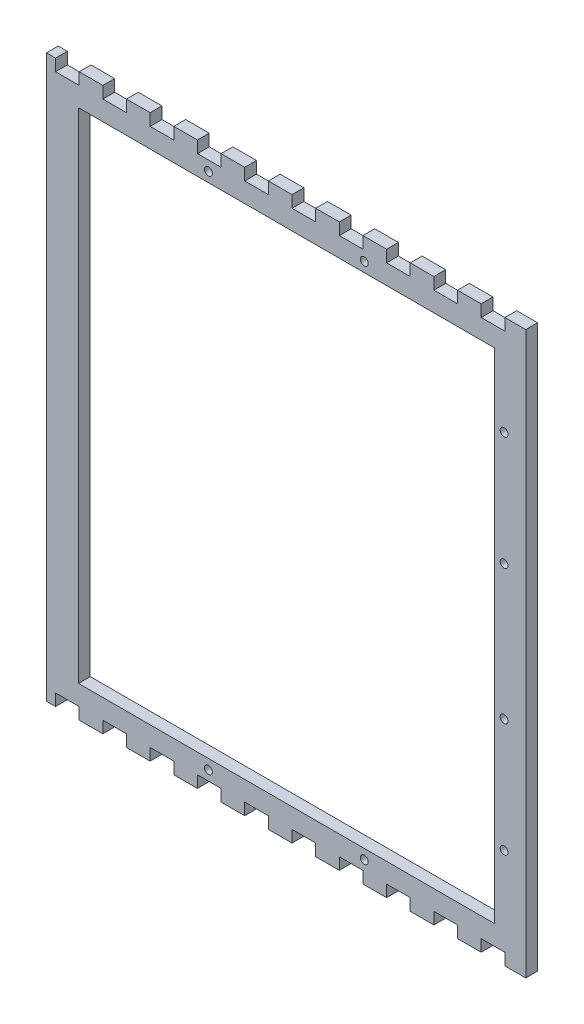
SolidWorks part; units mm, degrees
ref_plane "Front Plane" through (0, 0, 0) normal (0, 0, 1) x (1, 0, 0)
ref_plane "Top Plane" through (0, 0, 0) normal (0, 1, 0) x (1, 0, 0)
ref_plane "Right Plane" through (0, 0, 0) normal (1, 0, 0) x (0, 0, -1)
sketch "Model" plane through (0, 0, 0) normal (0, 0, 1) x (1, 0, 0)
  line L857 (1148.22, 22.8575) -> (1152.62, 22.8575)
  line L858 (1152.62, 22.8575) -> (1152.62, 28.5722)
  line L859 (1152.62, 28.5722) -> (1164.05, 28.5722)
  line L860 (1164.05, 28.5722) -> (1164.05, 22.8575)
  line L861 (1164.05, 22.8575) -> (1175.48, 22.8575)
  line L862 (1175.48, 22.8575) -> (1175.48, 28.5722)
  line L863 (1175.48, 28.5722) -> (1186.91, 28.5722)
  line L864 (1186.91, 28.5722) -> (1186.91, 22.8575)
  line L865 (1186.91, 22.8575) -> (1198.34, 22.8575)
  line L866 (1198.34, 22.8575) -> (1198.34, 28.5722)
  line L867 (1198.34, 28.5722) -> (1209.77, 28.5722)
  line L868 (1209.77, 28.5722) -> (1209.77, 22.8575)
  line L869 (1209.77, 22.8575) -> (1221.2, 22.8575)
  line L870 (1221.2, 22.8575) -> (1221.2, 28.5722)
  line L871 (1221.2, 28.5722) -> (1232.63, 28.5722)
  line L872 (1232.63, 28.5722) -> (1232.63, 22.8575)
  line L873 (1232.63, 22.8575) -> (1244.06, 22.8575)
  line L874 (1244.06, 22.8575) -> (1244.06, 28.5722)
  line L875 (1244.06, 28.5722) -> (1255.49, 28.5722)
  line L876 (1255.49, 28.5722) -> (1255.49, 22.8575)
  line L877 (1255.49, 22.8575) -> (1266.92, 22.8575)
  line L878 (1266.92, 22.8575) -> (1266.92, 28.5722)
  line L879 (1266.92, 28.5722) -> (1278.35, 28.5722)
  line L880 (1278.35, 28.5722) -> (1278.35, 22.8575)
  line L881 (1278.35, 22.8575) -> (1289.78, 22.8575)
  line L882 (1289.78, 22.8575) -> (1289.78, 28.5722)
  line L883 (1289.78, 28.5722) -> (1301.21, 28.5722)
  line L884 (1301.21, 28.5722) -> (1301.21, 22.8575)
  line L885 (1301.21, 22.8575) -> (1312.64, 22.8575)
  line L886 (1312.64, 22.8575) -> (1312.64, 28.5722)
  line L887 (1312.64, 28.5722) -> (1324.07, 28.5722)
  line L888 (1324.07, 28.5722) -> (1324.07, 22.8575)
  line L889 (1324.07, 22.8575) -> (1335.5, 22.8575)
  line L890 (1335.5, 22.8575) -> (1335.5, 28.5722)
  line L891 (1335.5, 28.5722) -> (1346.93, 28.5722)
  line L892 (1346.93, 28.5722) -> (1346.93, 22.8575)
  line L893 (1346.93, 22.8575) -> (1358.36, 22.8575)
  line L894 (1358.36, 22.8575) -> (1358.36, 28.5722)
  line L895 (1358.36, 28.5722) -> (1369.79, 28.5722)
  line L896 (1369.79, 28.5722) -> (1369.79, 22.8575)
  line L897 (1369.79, 22.8575) -> (1374.18, 22.8575)
  line L898 (1374.18, 22.8575) -> (1379.9, 22.8575)
  line L899 (1379.9, 22.8575) -> (1379.9, 28.5722)
  line L900 (1379.9, 28.5722) -> (1379.9, 288.572)
  line L901 (1379.9, 288.572) -> (1379.9, 294.287)
  line L902 (1379.9, 294.287) -> (1374.18, 294.287)
  line L903 (1374.18, 294.287) -> (1369.79, 294.287)
  line L904 (1369.79, 294.287) -> (1369.79, 288.572)
  line L905 (1369.79, 288.572) -> (1358.36, 288.572)
  line L906 (1358.36, 288.572) -> (1358.36, 294.287)
  line L907 (1358.36, 294.287) -> (1346.93, 294.287)
  line L908 (1346.93, 294.287) -> (1346.93, 288.572)
  line L909 (1346.93, 288.572) -> (1335.5, 288.572)
  line L910 (1335.5, 288.572) -> (1335.5, 294.287)
  line L911 (1335.5, 294.287) -> (1324.07, 294.287)
  line L912 (1324.07, 294.287) -> (1324.07, 288.572)
  line L913 (1324.07, 288.572) -> (1312.64, 288.572)
  line L914 (1312.64, 288.572) -> (1312.64, 294.287)
  line L915 (1312.64, 294.287) -> (1301.21, 294.287)
  line L916 (1301.21, 294.287) -> (1301.21, 288.572)
  line L917 (1301.21, 288.572) -> (1289.78, 288.572)
  line L918 (1289.78, 288.572) -> (1289.78, 294.287)
  line L919 (1289.78, 294.287) -> (1278.35, 294.287)
  line L920 (1278.35, 294.287) -> (1278.35, 288.572)
  line L921 (1278.35, 288.572) -> (1266.92, 288.572)
  line L922 (1266.92, 288.572) -> (1266.92, 294.287)
  line L923 (1266.92, 294.287) -> (1255.49, 294.287)
  line L924 (1255.49, 294.287) -> (1255.49, 288.572)
  line L925 (1255.49, 288.572) -> (1244.06, 288.572)
  line L926 (1244.06, 288.572) -> (1244.06, 294.287)
  line L927 (1244.06, 294.287) -> (1232.63, 294.287)
  line L928 (1232.63, 294.287) -> (1232.63, 288.572)
  line L929 (1232.63, 288.572) -> (1221.2, 288.572)
  line L930 (1221.2, 288.572) -> (1221.2, 294.287)
  line L931 (1221.2, 294.287) -> (1209.77, 294.287)
  line L932 (1209.77, 294.287) -> (1209.77, 288.572)
  line L933 (1209.77, 288.572) -> (1198.34, 288.572)
  line L934 (1198.34, 288.572) -> (1198.34, 294.287)
  line L935 (1198.34, 294.287) -> (1186.91, 294.287)
  line L936 (1186.91, 294.287) -> (1186.91, 288.572)
  line L937 (1186.91, 288.572) -> (1175.48, 288.572)
  line L938 (1175.48, 288.572) -> (1175.48, 294.287)
  line L939 (1175.48, 294.287) -> (1164.05, 294.287)
  line L940 (1164.05, 294.287) -> (1164.05, 288.572)
  line L941 (1164.05, 288.572) -> (1152.62, 288.572)
  line L942 (1152.62, 288.572) -> (1152.62, 294.287)
  line L943 (1152.62, 294.287) -> (1148.22, 294.287)
  line L944 (1148.22, 294.287) -> (1148.22, 288.572)
  line L945 (1148.22, 288.572) -> (1148.22, 28.5722)
  line L946 (1148.22, 28.5722) -> (1148.22, 22.8575)
extrude "Boss-Extrude1" add sketch "Model" along normal blind 5.715
sketch "Sketch1" plane through (0, 0, 0) normal (0, 0, -1) x (-1, 0, 0)
  line L8 (-1163.685, 279.0723) -> (-1364.685, 279.0723)
  line L9 (-1163.685, 38.0723) -> (-1163.685, 279.0723)
  line L10 (-1364.685, 38.0723) -> (-1163.685, 38.0723)
  line L11 (-1364.685, 279.0723) -> (-1364.685, 38.0723)
  line L12 (-1163.685, 279.0723) -> (-1364.685, 279.0723)
  line L13 (-1163.685, 38.0723) -> (-1163.685, 279.0723)
  line L14 (-1364.685, 38.0723) -> (-1163.685, 38.0723)
  line L15 (-1364.685, 279.0723) -> (-1364.685, 38.0723)
  dimension "D1" = 0.5
extrude "Cut-Extrude1" cut sketch "Sketch1" against normal through all
sketch "Sketch2" plane through (0, 0, 0) normal (0, 0, -1) x (-1, 0, 0)
  line L0 (-1364.075, 288.572) -> (-1364.075, 279.0723) construction
  line L1 (-1369.79, 288.572) -> (-1358.36, 288.572) construction
  line L2 (-1163.685, 279.0723) -> (-1364.685, 279.0723) construction
  line L3 (-1379.9, 283.8221) -> (-1148.22, 283.8221) construction
  line L4 (-1379.9, 22.8575) -> (-1379.9, 294.287) construction
  line L5 (-1148.22, 294.287) -> (-1148.22, 22.8575) construction
  line L6 (-1379.9, 158.5722) -> (-1148.22, 158.5722) construction
  line L7 (-1264.185, 271.0723) -> (-1264.185, 283.8221) construction
  line L8 (-1341.185, 271.0723) -> (-1291.8517, 271.0723) construction
  line L9 (-1341.185, 277.572) -> (-1341.185, 264.572) construction
  line L10 (-1291.8517, 277.572) -> (-1291.8517, 264.572) construction
  line L11 (-1301.8517, 271.0723) -> (-1301.8517, 283.8221) construction
  point P6 (-1364.075, 283.8221)
  point P15 (-1301.8517, 283.8221)
  point P16 (-1264.185, 271.0723)
  point P17 (-1301.8517, 271.0723)
  point P31 (-1226.5183, 283.8221)
  point P32 (-1226.5183, 33.3224)
  point P34 (-1301.8517, 33.3224)
  dimension "D1" = 10
hole_wizard "CSK for #6 Flat Head Machine Screw (100)1" positions "Sketch3" profile "Sketch4" countersink size "#6" standard "ANSI Inch" end condition through all
sketch "Sketch3" plane through (0, 0, 0) normal (0, 0, -1) x (-1, 0, 0)
  point P0 (-1301.8517, 283.8221)
  point P3 (-1226.5183, 283.8221)
  point P6 (-1226.5183, 33.3224)
  point P9 (-1301.8517, 33.3224)
sketch "Sketch4" plane through (1301.8517, 283.8221, 0) normal (1, 0, 0) x (0, 1, 0)
  line L0 (0, 0) -> (0, 5.715)
  line L1 (0, 5.715) -> (1.8986, 5.715)
  line L2 (1.8986, 5.715) -> (1.8986, 1.38)
  line L3 (1.8986, 1.38) -> (3.5433, 0)
  line L5 (3.5433, 0) -> (0, 0)
  line L6 (-1.8986, 1.38) -> (-3.5433, 0) construction
  line L11 (0, -6.35) -> (0, 107.95) construction
  dimension "Thru Hole Dia." = 3.7973
  dimension "Thru Hole Depth" = 5.715
  dimension "Near C'Sink Dia." = 7.0866
  dimension "Near C'Sink Angle" = 100
sketch "Sketch5" plane through (0, 0, 0) normal (0, 0, -1) x (-1, 0, 0)
  point P0 (-1369.435, 246.0721)
  point P1 (-1369.435, 191.0721)
  point P3 (-1369.435, 71.0721)
  point P5 (-1369.435, 126.0721)
hole_wizard "CSK for #6 Flat Head Machine Screw (100)2" positions "Sketch6" profile "Sketch7" countersink size "#6" standard "ANSI Inch" end condition through all
sketch "Sketch6" plane through (0, 0, 0) normal (0, 0, -1) x (-1, 0, 0)
  point P0 (-1369.435, 246.0721)
  point P3 (-1369.435, 191.0721)
  point P6 (-1369.435, 126.0721)
  point P9 (-1369.435, 71.0721)
sketch "Sketch7" plane through (1369.435, 246.0721, 0) normal (1, 0, 0) x (0, 1, 0)
  line L0 (0, 0) -> (0, 5.715)
  line L1 (0, 5.715) -> (1.8986, 5.715)
  line L2 (1.8986, 5.715) -> (1.8986, 1.38)
  line L3 (1.8986, 1.38) -> (3.5433, 0)
  line L5 (3.5433, 0) -> (0, 0)
  line L6 (-1.8986, 1.38) -> (-3.5433, 0) construction
  line L11 (0, -6.35) -> (0, 107.95) construction
  dimension "Thru Hole Dia." = 3.7973
  dimension "Thru Hole Depth" = 5.715
  dimension "Near C'Sink Dia." = 7.0866
  dimension "Near C'Sink Angle" = 100
